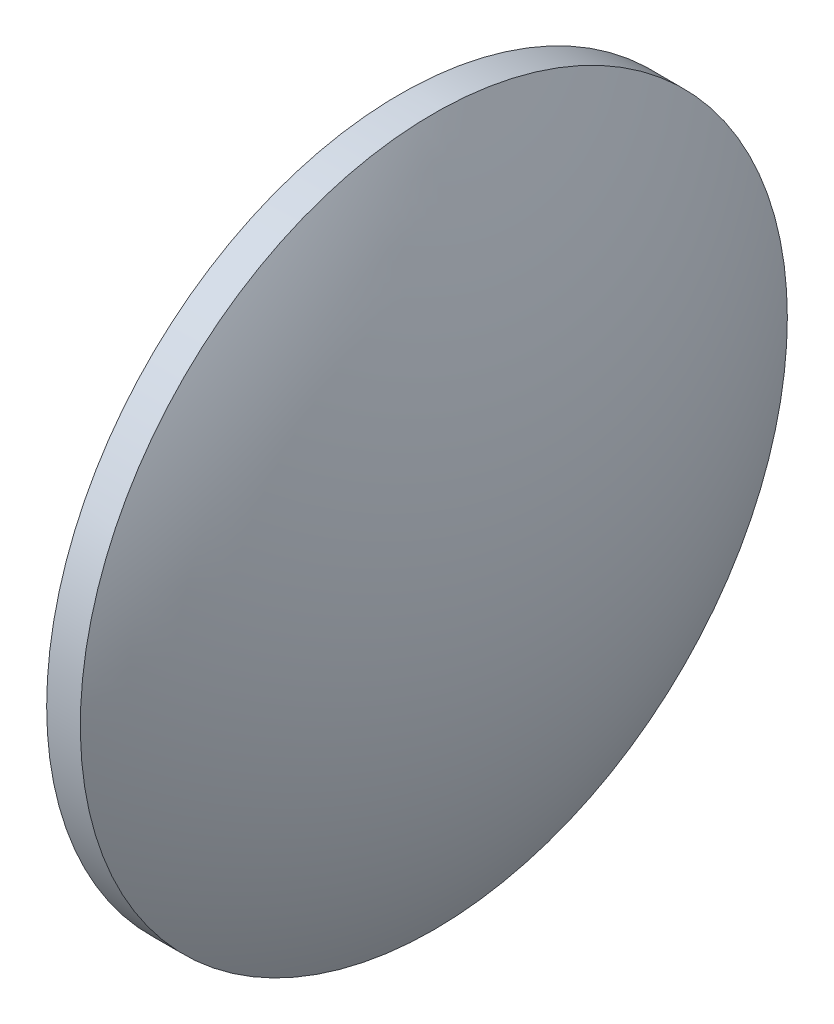
SolidWorks part; units mm, degrees
ref_plane "前视基准面" through (0, 0, 0) normal (0, 0, 1) x (1, 0, 0)
ref_plane "上视基准面" through (0, 0, 0) normal (0, 1, 0) x (1, 0, 0)
ref_plane "右视基准面" through (0, 0, 0) normal (1, 0, 0) x (0, 0, -1)
sketch "草图1" plane through (0, 0, 0) normal (0, 0, 1) x (1, 0, 0)
  line L0 (217.9946, 130.4671) -> (258.5717, 130.4671) construction
  line L1 (237.1753, 130.4671) -> (225.9653, 130.4671)
  line L6 (217.9946, 130.4671) -> (258.5717, 130.4671) construction
  line L7 (225.9653, 130.4671) -> (225.9653, 161.9671)
  line L8 (225.9653, 161.9671) -> (228.9653, 161.9671)
  arc A0 (237.1753, 130.4671) -> (228.9653, 161.9671) centre (172.641, 130.4671) ccw
revolve "旋转2" add sketch "草图1" angle 360 about L1
